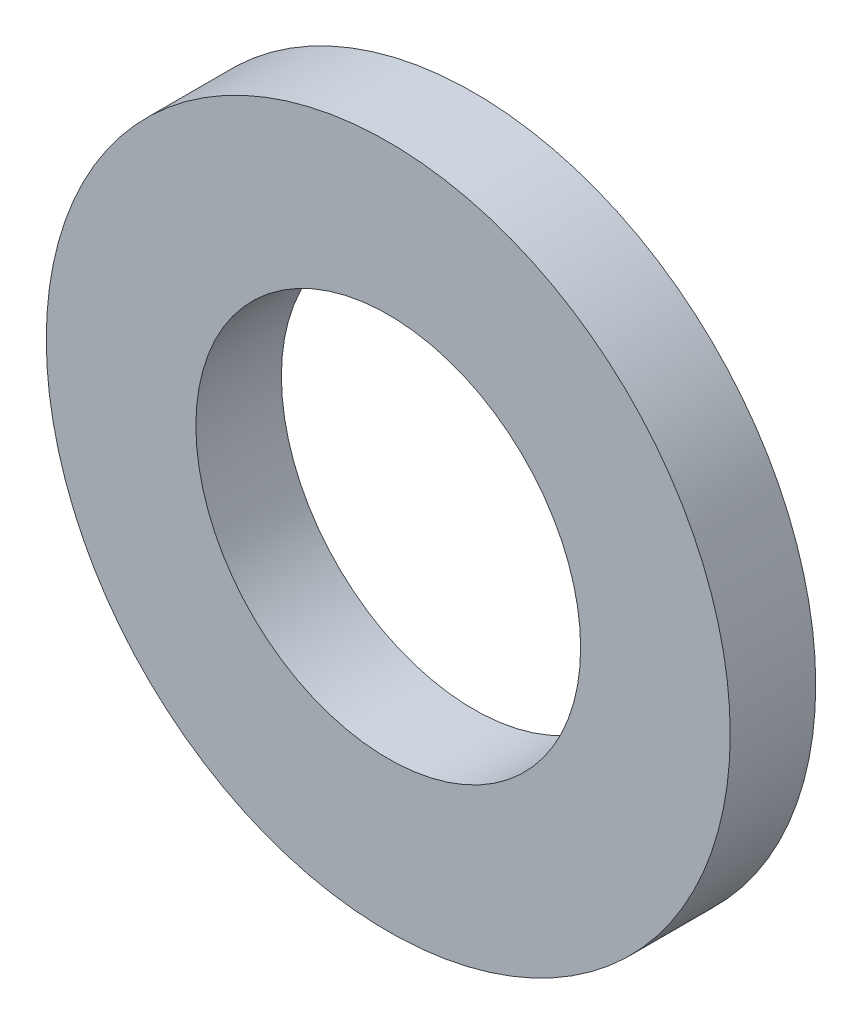
SolidWorks part; units mm, degrees
material "1060-O (SS)"
ref_plane "Ebene vorne" through (0, 0, 0) normal (0, 0, 1) x (1, 0, 0)
ref_plane "Ebene oben" through (0, 0, 0) normal (0, 1, 0) x (1, 0, 0)
ref_plane "Ebene rechts" through (0, 0, 0) normal (1, 0, 0) x (0, 0, -1)
sketch "Sketch1" plane through (0, 0, 0) normal (0, 0, 1) x (1, 0, 0)
  circle A0 centre (0, 0) radius 2.25
  circle A1 centre (0, 0) radius 4
  dimension "D1" = 8
  dimension "D2" = 4.5
extrude "Boss-Extrude1" add sketch "Sketch1" along normal blind 1
equation "\"¨8\"=220"
